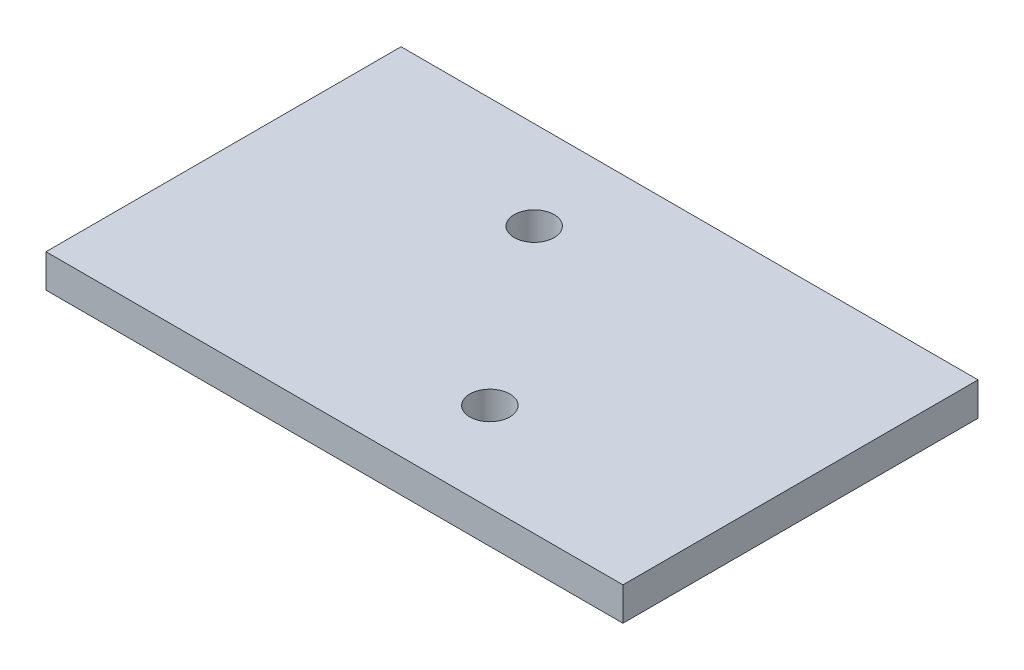
SolidWorks part; units mm, degrees
ref_plane "Front Plane" through (0, 0, 0) normal (0, 0, 1) x (1, 0, 0)
ref_plane "Top Plane" through (0, 0, 0) normal (0, 1, 0) x (1, 0, 0)
ref_plane "Right Plane" through (0, 0, 0) normal (1, 0, 0) x (0, 0, -1)
sketch "Base Sketch" plane through (0, 0, 0) normal (0, 1, 0) x (1, 0, 0)
  line L1 (-13, -8) -> (13, -8)
  line L2 (-13, -8) -> (-13, 8)
  line L3 (-13, 8) -> (13, 8)
  line L4 (13, -8) -> (13, 8)
  line L5 (-13, -8) -> (13, 8) construction
  line L6 (-13, 8) -> (13, -8) construction
  point P0 (0, 0)
  dimension "D1" = 26
  dimension "D2" = 16
extrude "Boss-Extrude1" add sketch "Base Sketch" along normal blind 1.5
sketch "2 Hole Locations" plane through (0, 0, 0) normal (0, 1, 0) x (1, 0, 0)
  line L0 (13, 8) -> (-13, 8) construction
  line L1 (-13, -8) -> (13, -8) construction
  line L3 (13, -8) -> (13, 8) construction
  line L4 (-13, 8) -> (-13, -8) construction
  point P0 (-3, 4)
  point P1 (3, -4)
  point P6 (0, 0)
  point P8 (13, -5.8566)
  dimension "D1" = 4
  dimension "D2" = 4
  dimension "D3" = 10
  dimension "D4" = 10
hole_wizard "Ø1.8 (1.8) Diameter Hole1" positions "Sketch3" profile "Sketch4" hole size "Ø1.8" standard "ANSI Metric" end condition through all
sketch "Sketch3" plane through (0, 1.5, 0) normal (0, 1, 0) x (1, 0, 0)
  point P0 (-3, 4)
  point P3 (3, -4)
sketch "Sketch4" plane through (-3, 1.5, -4) normal (1, 0, 0) x (0, 0, 1)
  line L0 (0, 0) -> (0, 1.5)
  line L1 (0, 1.5) -> (0.9, 1.5)
  line L2 (0.9, 1.5) -> (0.9, 0)
  line L5 (0.9, 0) -> (0, 0)
  line L11 (0, -6.35) -> (0, 107.95) construction
  dimension "Thru Hole Dia." = 1.8
  dimension "Thru Hole Depth" = 1.5
